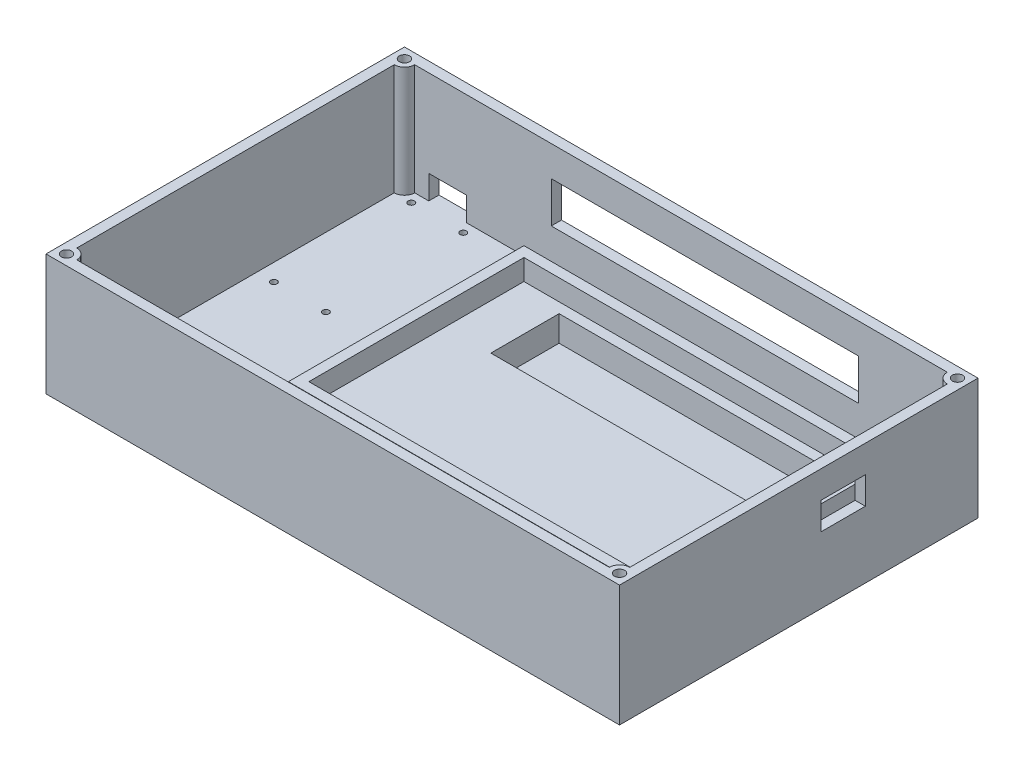
SolidWorks part; units mm, degrees
ref_plane "Front Plane" through (0, 0, 0) normal (0, 0, 1) x (1, 0, 0)
ref_plane "Top Plane" through (0, 0, 0) normal (0, 1, 0) x (1, 0, 0)
ref_plane "Right Plane" through (0, 0, 0) normal (1, 0, 0) x (0, 0, -1)
sketch "Sketch1" plane through (0, 0, 0) normal (0, 1, 0) x (1, 0, 0)
  line L26 (0, 0) -> (168, 0)
  line L27 (0, 0) -> (0, 105)
  line L28 (0, 105) -> (168, 105)
  line L29 (168, 0) -> (168, 105)
  dimension "D1" = 168
  dimension "D2" = 105
extrude "Boss-Extrude1" add sketch "Sketch1" along normal blind 35.5
shell "Shell3" thickness 3
sketch "Sketch3" plane through (0, 3, 0) normal (0, 1, 0) x (1, 0, 0)
  line L0 (3, 102) -> (3, 3) construction
  line L1 (165, 102) -> (3, 102) construction
  line L2 (15.615, 102) -> (15.615, 57.11) construction
  line L3 (165, 102) -> (3, 102) construction
  line L4 (6.73, 78.88) -> (24.5, 78.88) construction
  line L5 (165, 102) -> (3, 102) construction
  circle A0 centre (8, 99) radius 0.925
  circle A1 centre (23.23, 99) radius 0.925
  circle A2 centre (23.23, 58.76) radius 0.925
  circle A3 centre (8, 58.76) radius 0.925
  point P14 (15.615, 78.88)
  dimension "D3" = 1.85
  dimension "D1" = 5
  dimension "D2" = 3
  dimension "D4" = 17.77
  dimension "D5" = 44.89
  dimension "D6" = 3.73
  dimension "D7" = 23.12
extrude "Cut-Extrude2" cut sketch "Sketch3" against normal up to surface (3 mm away) up to face at (84, 0, -52.5)
sketch "Sketch7" plane through (0, 3, 0) normal (0, 1, 0) x (1, 0, 0)
  line L0 (155, 88) -> (155, 25)
  line L1 (165, 102) -> (40, 102) construction
  line L2 (165, 102) -> (165, 20) construction
  line L3 (165, 20) -> (40, 20) construction
  line L4 (40, 102) -> (40, 20) construction
  line L5 (155, 25) -> (52, 25)
  line L6 (52, 25) -> (52, 88)
  line L7 (52, 88) -> (155, 88)
  line L8 (49, 91) -> (158, 91)
  line L9 (158, 91) -> (158, 22)
  line L10 (158, 22) -> (49, 22)
  line L11 (49, 22) -> (49, 91)
  dimension "D1" = 125
  dimension "D2" = 82
  dimension "D3" = 103
  dimension "D4" = 63
  dimension "D5" = 10
  dimension "D6" = 5
  dimension "D7" = 3
extrude "Boss-Extrude3" add sketch "Sketch7" along normal blind 13.6 contours L11 L10 L9 L8 L6 L7 L0 L5
sketch "Sketch8" plane through (0, 3, 0) normal (0, 1, 0) x (1, 0, 0)
  line L1 (65.3, 85) -> (140.3, 85)
  line L2 (65.3, 85) -> (65.3, 65)
  line L3 (65.3, 65) -> (140.3, 65)
  line L4 (52, 88) -> (52, 25)
  line L5 (52, 25) -> (155, 25)
  line L6 (155, 25) -> (155, 88)
  line L7 (155, 88) -> (52, 88)
  line L8 (52, 88) -> (52, 25)
  line L9 (52, 25) -> (155, 25)
  line L10 (155, 25) -> (155, 88)
  line L11 (155, 88) -> (52, 88)
  line L12 (140.3, 85) -> (140.3, 65)
  dimension "D2" = 75
  dimension "D3" = 20
  dimension "D4" = 3
  dimension "D5" = 13.3
  dimension "D1" = 0
extrude "Boss-Extrude4" add sketch "Sketch8" along normal blind 7.5
sketch "Sketch2" plane through (0, 0, -105) normal (0, 0, -1) x (-1, 0, 0)
  line L0 (-158, 3) -> (-49, 3) construction
  line L1 (-10.115, 3) -> (-21.115, 3)
  line L2 (-10.115, 3) -> (-10.115, 10)
  line L3 (-10.115, 10) -> (-21.115, 10)
  line L4 (-21.115, 3) -> (-21.115, 10)
  line L6 (-15.615, 10) -> (-15.615, 3) construction
  line L7 (-168, 35.5) -> (0, 35.5) construction
  line L9 (-49, 16.6) -> (-49, 3) construction
  line L10 (-3, 35.5) -> (-3, 3) construction
  line L12 (-46, 14.6) -> (-136, 14.6)
  line L13 (-46, 14.6) -> (-46, 26.6)
  line L14 (-46, 26.6) -> (-136, 26.6)
  line L15 (-136, 14.6) -> (-136, 26.6)
  dimension "D1" = 11
  dimension "D2" = 7
  dimension "D3" = 12.615
  dimension "D4" = 12
  dimension "D5" = 90
  dimension "D6" = 8.9
  dimension "D7" = 3
extrude "Cut-Extrude1" cut sketch "Sketch2" against normal up to surface (3 mm away) up to face at (84, 19.25, -102)
sketch "Sketch4" plane through (0, 3, 0) normal (0, 1, 0) x (1, 0, 0)
  line L0 (10.115, 102) -> (3, 102) construction
  line L1 (3, 102) -> (3, 3) construction
  line L2 (6, 102) -> (3, 102)
  line L3 (3, 102) -> (3, 99)
  line L4 (84, 102) -> (84, 3) construction
  line L5 (165, 102) -> (3, 102) construction
  line L6 (3, 3) -> (165, 3) construction
  line L7 (165, 52.5) -> (3, 52.5) construction
  line L8 (165, 3) -> (165, 102) construction
  line L9 (162, 102) -> (165, 102)
  line L10 (165, 102) -> (165, 99)
  line L11 (165, 3) -> (165, 6)
  line L12 (162, 3) -> (165, 3)
  line L13 (6, 3) -> (3, 3)
  line L14 (3, 3) -> (3, 6)
  arc A0 (6, 102) -> (3, 99) centre (3, 102) cw
  arc A1 (162, 102) -> (165, 99) centre (165, 102) ccw
  arc A2 (162, 3) -> (165, 6) centre (165, 3) cw
  arc A3 (6, 3) -> (3, 6) centre (3, 3) ccw
  dimension "D1" = 3
extrude "Boss-Extrude2" add sketch "Sketch4" along normal up to surface (32.5 mm away) up to face at (84, 35.5, -52.5)
sketch "Sketch5" plane through (0, 35.5, 0) normal (0, 1, 0) x (1, 0, 0)
  line L0 (84, 105) -> (84, 0) construction
  line L1 (168, 105) -> (0, 105) construction
  line L2 (0, 0) -> (168, 0) construction
  line L3 (168, 52.5) -> (0, 52.5) construction
  line L4 (168, 0) -> (168, 105) construction
  line L5 (0, 105) -> (0, 0) construction
  circle A0 centre (3, 102) radius 1.5
  arc A1 (3, 99) -> (6, 102) centre (3, 102) ccw construction
  circle A2 centre (165, 102) radius 1.5
  circle A3 centre (3, 3) radius 1.5
  circle A4 centre (165, 3) radius 1.5
  dimension "D1" = 3
extrude "Cut-Extrude3" cut sketch "Sketch5" against normal offset from surface (29.5 mm away) 6 up to face at (8, 0, -59.685)
sketch "Sketch13" plane through (168, 0, 0) normal (1, 0, 0) x (0, 0, -1)
  line L0 (0, 35.5) -> (105, 35.5) construction
  line L1 (72, 19.5) -> (59, 19.5)
  line L2 (72, 19.5) -> (72, 27.5)
  line L3 (72, 27.5) -> (59, 27.5)
  line L4 (59, 19.5) -> (59, 27.5)
  dimension "D1" = 16
  dimension "D2" = 13
  dimension "D3" = 19
  dimension "D4" = 8
extrude "Cut-Extrude8" cut sketch "Sketch13" against normal up to surface (3 mm away) up to face at (165, 19.25, -52.5)
sketch "Sketch14" plane through (0, 0, -105) normal (0, 0, -1) x (-1, 0, 0)
  line L0 (-137, 0) -> (-137, 35.5)
  line L1 (-168, 0) -> (0, 0) construction
  line L2 (-168, 35.5) -> (0, 35.5) construction
  line L3 (-137, 35.5) -> (-45, 35.5)
  line L4 (-45, 35.5) -> (-45, 0)
  line L5 (-45, 0) -> (-137, 0)
  line L6 (-136, 26.6) -> (-136, 14.6) construction
  line L8 (-46, 14.6) -> (-46, 26.6) construction
  dimension "D1" = 1
  dimension "D2" = 1
extrude "Cut-Extrude9" [suppressed] cut sketch "Sketch14" against normal through all flip side to cut
sketch "Sketch15" [suppressed] plane through (0, 0, 0) normal (0, 1, 0) x (1, 0, 0)
  line L1 (129, 0) -> (40, 0)
  line L2 (129, 0) -> (129, 99)
  line L3 (129, 99) -> (40, 99)
  line L4 (40, 0) -> (40, 99)
extrude "Cut-Extrude11" [suppressed] cut sketch "Sketch15" along normal through all
